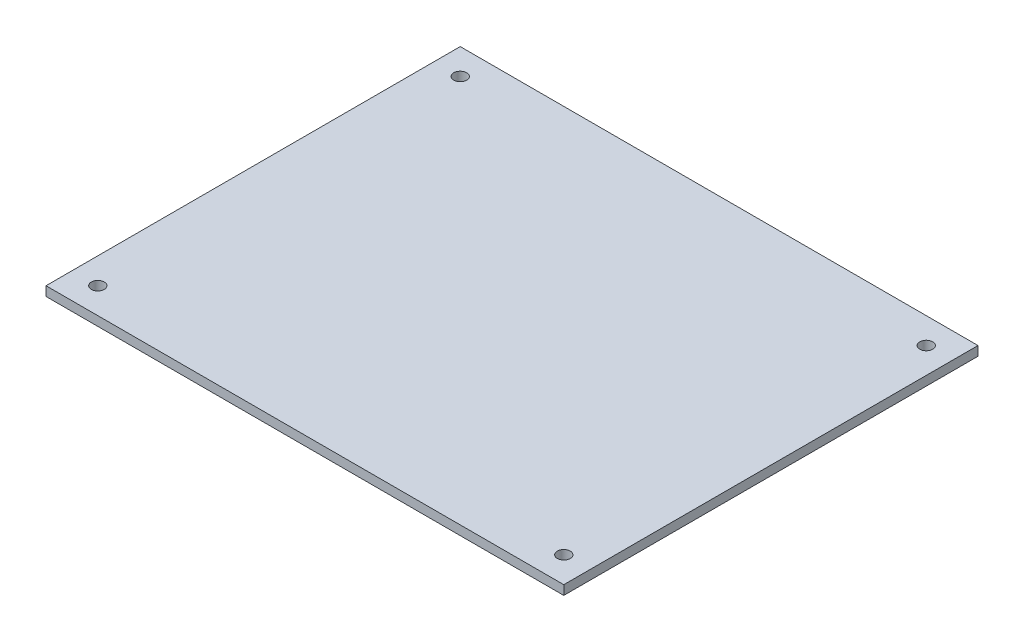
SolidWorks part; units mm, degrees
ref_plane "Front Plane" through (0, 0, 0) normal (0, 0, 1) x (1, 0, 0)
ref_plane "Top Plane" through (0, 0, 0) normal (0, 1, 0) x (1, 0, 0)
ref_plane "Right Plane" through (0, 0, 0) normal (1, 0, 0) x (0, 0, -1)
sketch "Sketch1" plane through (0, 0, 0) normal (0, 1, 0) x (1, 0, 0)
  line L1 (-50, -40) -> (50, -40)
  line L2 (-50, -40) -> (-50, 40)
  line L3 (-50, 40) -> (50, 40)
  line L4 (50, -40) -> (50, 40)
  line L5 (-50, -40) -> (50, 40) construction
  line L6 (-50, 40) -> (50, -40) construction
  point P0 (0, 0)
  dimension "D1" = 100
  dimension "D2" = 80
extrude "Boss-Extrude1" add sketch "Sketch1" along normal blind 1.8
sketch "Sketch2" plane through (0, 1.8, 0) normal (0, 1, 0) x (1, 0, 0)
  line L0 (-50, 40) -> (-50, -40) construction
  line L1 (50, 40) -> (-50, 40) construction
  line L2 (50, -40) -> (50, 40) construction
  line L3 (-50, -40) -> (50, -40) construction
  circle A0 centre (-45, -35) radius 1.25
  circle A1 centre (-45, 35) radius 1.25
  circle A2 centre (45, 35) radius 1.25
  circle A3 centre (45, -35) radius 1.25
  point P12 (-43.4017, 40)
  point P17 (-45.8449, -38.8103)
  dimension "D1" = 2.5
  dimension "D6" = 2.5
  dimension "D7" = 5
  dimension "D9" = 2.5
  dimension "D10" = 2.5
  dimension "D11" = 5
  dimension "D12" = 5
  dimension "D2" = 5
  dimension "D3" = 5
  dimension "D4" = 5
  dimension "D5" = 5
  dimension "D8" = 5
extrude "Cut-Extrude1" cut sketch "Sketch2" against normal through all
